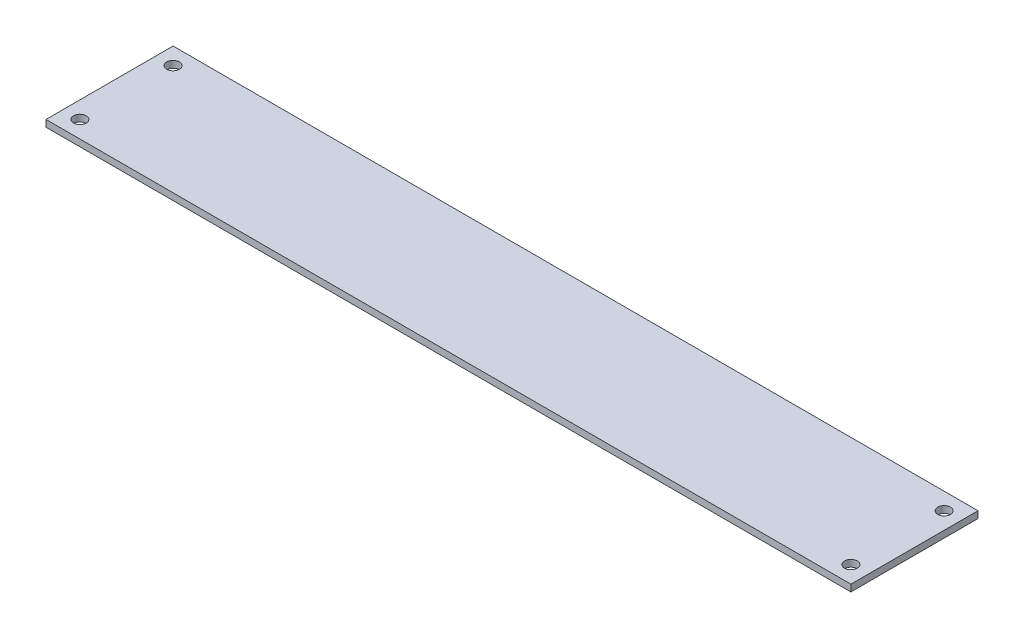
SolidWorks part; units mm, degrees
ref_plane "Ebene vorne" through (0, 0, 0) normal (0, 0, 1) x (1, 0, 0)
ref_plane "Ebene oben" through (0, 0, 0) normal (0, 1, 0) x (1, 0, 0)
ref_plane "Ebene rechts" through (0, 0, 0) normal (1, 0, 0) x (0, 0, -1)
sketch "Sketch2" plane through (0, 0, 0) normal (0, 1, 0) x (1, 0, 0)
  line L1 (-95, -15) -> (95, -15)
  line L2 (-95, -15) -> (-95, 15)
  line L3 (-95, 15) -> (95, 15)
  line L4 (95, -15) -> (95, 15)
  line L5 (-95, -15) -> (95, 15) construction
  line L6 (-95, 15) -> (95, -15) construction
  point P0 (0, 0)
  dimension "D1" = 30
  dimension "D2" = 190
extrude "Boss-Extrude1" add sketch "Sketch2" along normal blind 1.6
sketch "Sketch4" plane through (0, 1.6, 0) normal (0, 1, 0) x (1, 0, 0)
  line L0 (95, 15) -> (95, 11)
  line L1 (95, -15) -> (95, 15) construction
  line L2 (95, 11) -> (91, 11)
  circle A0 centre (91, 11) radius 1.5
  dimension "D3" = 3
  dimension "D1" = 4
  dimension "D2" = 4
extrude "Cut-Extrude2" cut sketch "Sketch4" against normal blind 1.6 contours A0
mirror "Mirror1" about plane through (0, 0, 0) normal (0, 0, 1) of "Cut-Extrude2"
mirror "Mirror2" about plane through (0, 0, 0) normal (1, 0, 0) of "Mirror1", "Cut-Extrude2"
